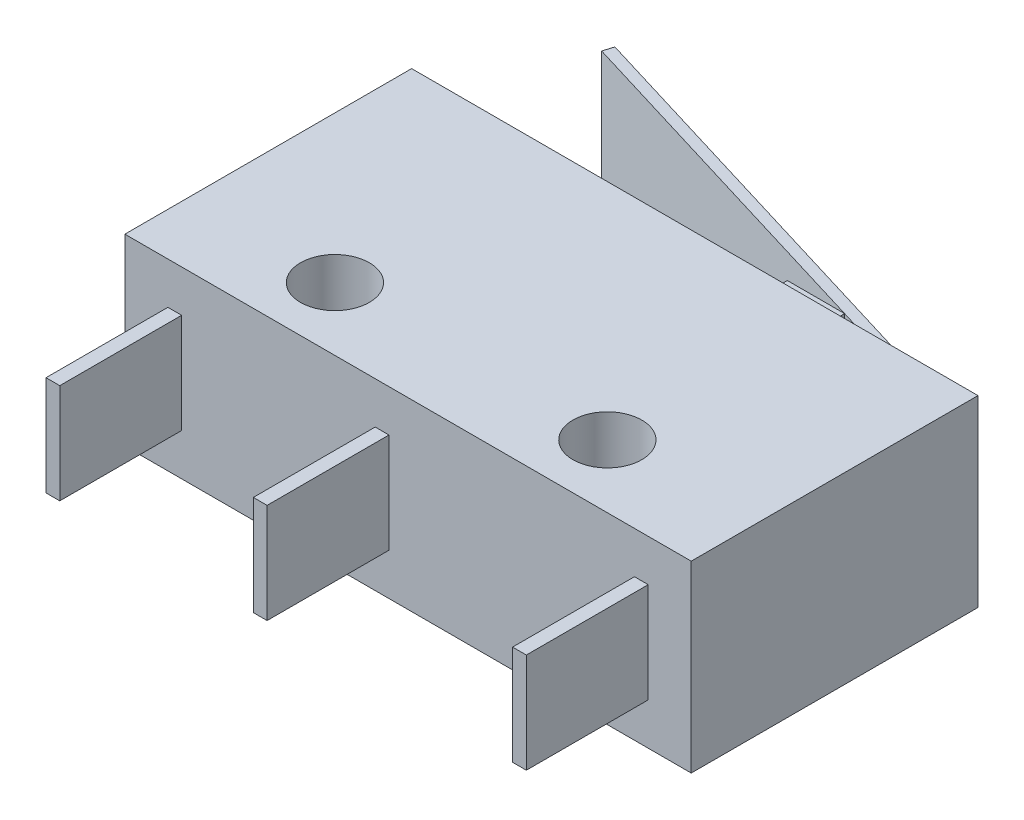
SolidWorks part; units mm, degrees
ref_plane "Front Plane" through (0, 0, 0) normal (0, 0, 1) x (1, 0, 0)
ref_plane "Top Plane" through (0, 0, 0) normal (0, 1, 0) x (1, 0, 0)
ref_plane "Right Plane" through (0, 0, 0) normal (1, 0, 0) x (0, 0, -1)
sketch "Sketch2" plane through (0, 0, 0) normal (0, 1, 0) x (1, 0, 0)
  line L1 (0, 0) -> (19.75, 0)
  line L2 (0, 0) -> (0, 10)
  line L3 (0, 10) -> (19.75, 10)
  line L4 (19.75, 0) -> (19.75, 10)
  line L5 (0, 0) -> (19.75, 10) construction
  line L6 (0, 10) -> (19.75, 0) construction
  circle A2 centre (5.125, 2.2) radius 1.2
  circle A3 centre (14.625, 2.2) radius 1.2
  point P4 (9.875, 5)
  point P10 (15.825, 2.2)
  point P11 (13.425, 2.2)
  point P12 (6.325, 2.2)
  point P13 (3.925, 2.2)
  point P14 (5.125, 3.4)
  point P16 (5.125, 1)
  dimension "D3" = 2.4
  dimension "D6" = 1
  dimension "D1" = 19.75
  dimension "D2" = 10
  dimension "D4" = 3.925
  dimension "D5" = 7.1
extrude "Boss-Extrude1" add sketch "Sketch2" along normal blind 6.4 contours L2 L3 L4 L1
sketch "Sketch3" plane through (0, 0, 0) normal (0, 0, 1) x (1, 0, 0)
  line L0 (0, 6.4) -> (0, 0) construction
  line L1 (1.5, 4.94) -> (1.98, 4.94)
  line L2 (1.5, 4.94) -> (1.5, 1.46)
  line L3 (1.5, 1.46) -> (1.98, 1.46)
  line L4 (1.98, 4.94) -> (1.98, 1.46)
  line L5 (1.5, 4.94) -> (1.98, 1.46) construction
  line L6 (1.5, 1.46) -> (1.98, 4.94) construction
  line L7 (8.73, 4.94) -> (9.21, 4.94)
  line L8 (8.73, 4.94) -> (8.73, 1.46)
  line L9 (8.73, 1.46) -> (9.21, 1.46)
  line L10 (9.21, 4.94) -> (9.21, 1.46)
  line L11 (8.73, 4.94) -> (9.21, 1.46) construction
  line L12 (8.73, 1.46) -> (9.21, 4.94) construction
  line L13 (17.77, 4.94) -> (18.25, 4.94)
  line L14 (17.77, 4.94) -> (17.77, 1.46)
  line L15 (17.77, 1.46) -> (18.25, 1.46)
  line L16 (18.25, 4.94) -> (18.25, 1.46)
  line L17 (17.77, 4.94) -> (18.25, 1.46) construction
  line L18 (17.77, 1.46) -> (18.25, 4.94) construction
  line L19 (19.75, 6.4) -> (19.75, 0) construction
  point P4 (1.74, 3.2)
  point P9 (8.97, 3.2)
  point P14 (18.01, 3.2)
  point P23 (0, 3.2)
  dimension "D1" = 0.48
  dimension "D2" = 3.48
  dimension "D3" = 1.5
  dimension "D4" = 1.5
  dimension "D5" = 6.75
extrude "Boss-Extrude2" add sketch "Sketch3" along normal blind 4.25
ref_plane "Plane1" through (0, 3.2, 0) normal (0, 1, 0) x (1, 0, 0)
sketch "Sketch4" plane through (0, 3.2, 0) normal (0, 1, 0) x (1, 0, 0)
  line L0 (19.75, 10) -> (0, 10) construction
  line L1 (13.75, 10) -> (11.75, 10)
  line L2 (13.75, 10) -> (13.75, 11.35)
  line L3 (13.75, 11.35) -> (11.75, 11.35)
  line L4 (11.75, 10) -> (11.75, 11.35)
  line L5 (13.75, 10) -> (11.75, 11.35) construction
  line L6 (13.75, 11.35) -> (11.75, 10) construction
  line L7 (16.63, 10) -> (16.63, 10.4757)
  line L8 (16.63, 10.4757) -> (1.5825, 15.044)
  line L9 (1.5825, 15.044) -> (1.69, 15.398)
  line L10 (1.69, 15.398) -> (17, 10.75)
  line L11 (17, 10.75) -> (17, 10)
  line L12 (17, 10) -> (16.63, 10)
  line L13 (19.75, 0) -> (19.75, 10) construction
  point P4 (12.75, 10.675)
  dimension "D1" = 2
  dimension "D2" = 1.35
  dimension "D3" = 0.75
  dimension "D4" = 6
  dimension "D5" = 2.75
  dimension "D6" = 0.37
  dimension "D7" = 16
extrude "Boss-Extrude4" add sketch "Sketch4" along normal blind 2 and the other way blind 2 separate body contours L4 L1 L2 L3 | L8 L9 L10 L11 L12 L7
